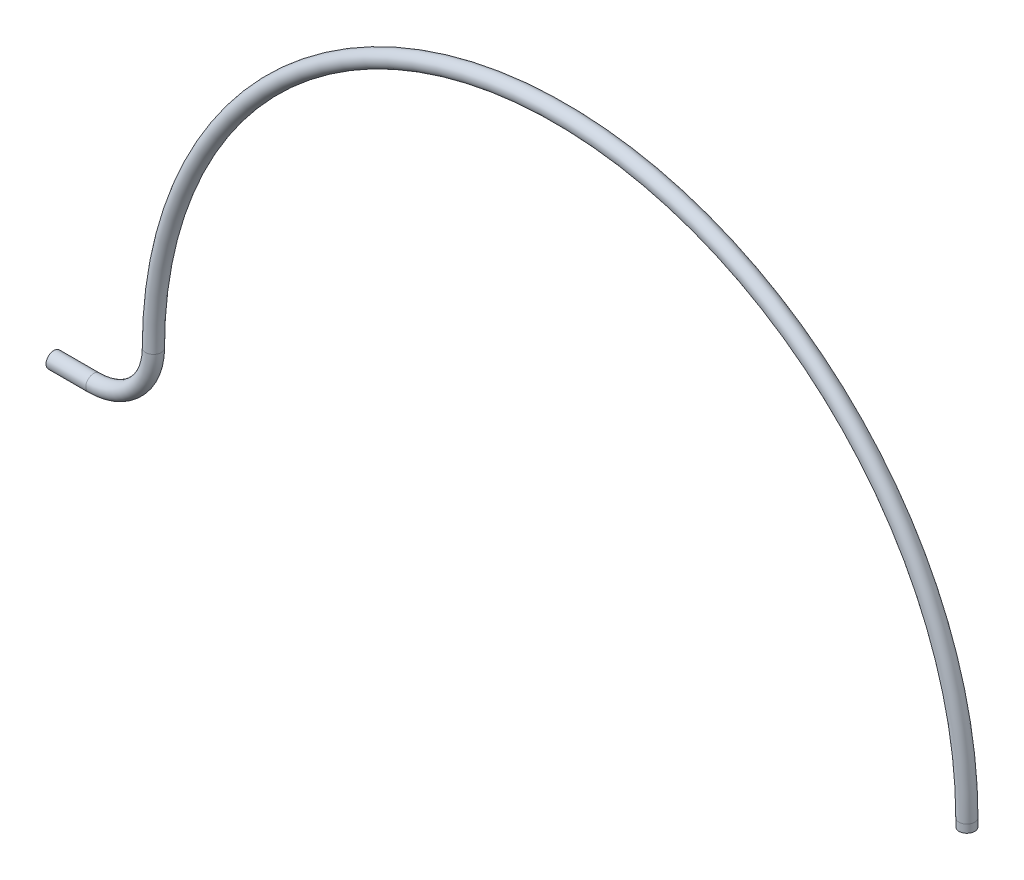
SolidWorks part; units mm, degrees
ref_plane "Front Plane" through (0, 0, 0) normal (0, 0, 1) x (1, 0, 0)
ref_plane "Top Plane" through (0, 0, 0) normal (0, 1, 0) x (1, 0, 0)
ref_plane "Right Plane" through (0, 0, 0) normal (1, 0, 0) x (0, 0, -1)
sketch "Sketch1" plane through (0, 0, 0) normal (0, 0, 1) x (1, 0, 0)
  line L0 (-922.4028, -43.1051) -> (-912.4028, -43.1051)
  line L1 (-693.0356, -28.1043) -> (-693.0356, -30.1043)
  line L2 (-693.0356, -4.1051) -> (-693.0356, -25.1051) construction
  line L6 (-939.1105, -43.1051) -> (-939.6638, -43.1051) construction
  arc A0 (-912.4028, -43.1051) -> (-897.4028, -28.105) centre (-912.4028, -28.1051) ccw
  arc A1 (-897.4028, -28.105) -> (-693.0356, -28.1043) centre (-795.2192, -28.1043) cw
  dimension "D1" = 2
  dimension "D2" = 15
  dimension "D3" = 10
ref_plane "Plane1" through (-922.4028, -43.1051, 0) normal (1, 0, 0) x (0, 0, -1)
sketch "Sketch2" plane through (-922.4028, -43.1051, 0) normal (1, 0, 0) x (0, 0, -1)
  circle A2 centre (0, 0) radius 0.95
  circle A3 centre (0, 0) radius 1.975
  dimension "D1" = 1.9
  dimension "D2" = 3.95
sweep "Sweep1" add profiles "Sketch2" path "Sketch1"
